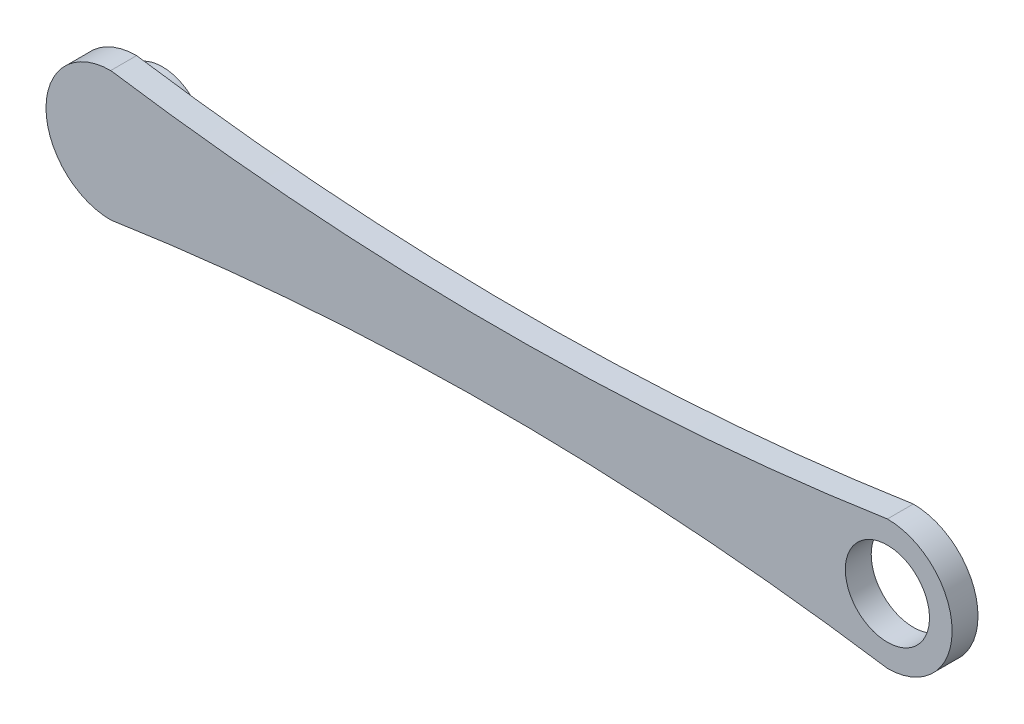
SolidWorks part; units mm, degrees
ref_plane "Front Plane" through (0, 0, 0) normal (0, 0, 1) x (1, 0, 0)
ref_plane "Top Plane" through (0, 0, 0) normal (0, 1, 0) x (1, 0, 0)
ref_plane "Right Plane" through (0, 0, 0) normal (1, 0, 0) x (0, 0, -1)
sketch "Sketch1" plane through (0, 0, 0) normal (0, 0, 1) x (1, 0, 0)
  line L0 (-150, 0) -> (150, 0) construction
  line L1 (-150, -25) -> (150, -25) construction
  line L3 (-150, 25) -> (150, 25) construction
  line L5 (-150, -25) -> (150, 25) construction
  line L6 (-150, 25) -> (150, -25) construction
  arc A0 (-150, 25) -> (-150, -25) centre (-150, 0) ccw
  arc A1 (150, -25) -> (150, 25) centre (150, 0) ccw
  arc A2 (-150, 25) -> (150, 25) centre (0, 1013.686) ccw
  arc A3 (-150, -25) -> (150, -25) centre (0, -1013.686) cw
  point P0 (0, 0)
  dimension "D4" = 25
  dimension "D6" = 1000
  dimension "D1" = 300
  dimension "D2" = 50
  dimension "D3" = 150
extrude "Boss-Extrude1" add sketch "Sketch1" along normal blind 10
sketch "Sketch3" plane through (0, 0, 10) normal (0, 0, 1) x (1, 0, 0)
  circle A1 centre (150, 0) radius 16.25
  dimension "D2" = 32.5
  dimension "D1" = 150
sketch "Sketch2" plane through (0, 0, 0) normal (0, 0, -1) x (1, 0, 0)
  circle A0 centre (-150, 0) radius 16.25
  dimension "D2" = 150
  dimension "D1" = 32.5
extrude "Boss-Extrude2" add sketch "Sketch2" along normal blind 10
extrude "Cut-Extrude4" cut sketch "Sketch3" against normal blind 10
